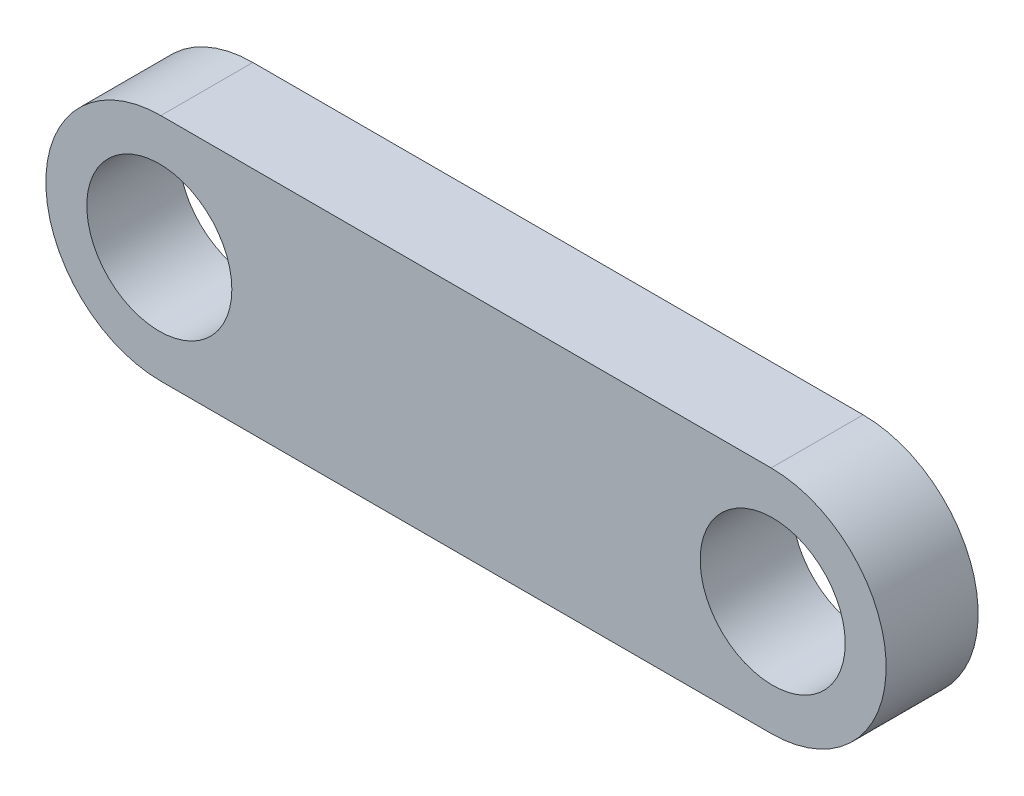
SolidWorks part; units mm, degrees
material "Acrylic (Medium-high impact)"
ref_plane "Front Plane" through (0, 0, 0) normal (0, 0, 1) x (1, 0, 0)
ref_plane "Top Plane" through (0, 0, 0) normal (0, 1, 0) x (1, 0, 0)
ref_plane "Right Plane" through (0, 0, 0) normal (1, 0, 0) x (0, 0, -1)
sketch "Sketch1" plane through (0, 0, 0) normal (0, 0, 1) x (1, 0, 0)
  line L0 (0, 0) -> (20, 0) construction
  line L1 (0, 3) -> (20, 3)
  line L2 (0, -3) -> (20, -3)
  arc A0 (0, 3) -> (0, -3) centre (0, 0) ccw
  arc A1 (20, -3) -> (20, 3) centre (20, 0) ccw
  circle A2 centre (0, 0) radius 2.395
  circle A3 centre (20, 0) radius 2.395
  point P3 (10, 0)
  dimension "D1" = 3
  dimension "D2" = 4.79
  dimension "D3" = 4.79
  dimension "D4" = 20
extrude "Boss-Extrude1" add sketch "Sketch1" along normal blind 3
sketch "Sketch2" plane through (0, 0, 3) normal (0, 0, 1) x (1, 0, 0)
  line L0 (10, 3) -> (10, -3) construction
  line L1 (20, 3) -> (0, 3) construction
  line L2 (0, -3) -> (20, -3) construction
  line L3 (0.05, 0) -> (19.95, 0) construction
  line L4 (0.05, 3.75) -> (19.95, 3.75)
  line L5 (0.05, -3.75) -> (19.95, -3.75)
  line L6 (20, 0) -> (23.7, 0) construction
  arc A0 (0.05, 3.75) -> (0.05, -3.75) centre (0.05, 0) ccw
  arc A1 (19.95, -3.75) -> (19.95, 3.75) centre (19.95, 0) ccw
  circle A2 centre (0, 0) radius 2.365
  circle A3 centre (20, 0) radius 2.365
  point P8 (10, 0)
  dimension "D2" = 4.73
  dimension "D1" = 3.7
  dimension "D4" = 7.5
extrude "Boss-Extrude2" add sketch "Sketch2" against normal up to surface (3 mm away) up to face at (10, 0, 0)
